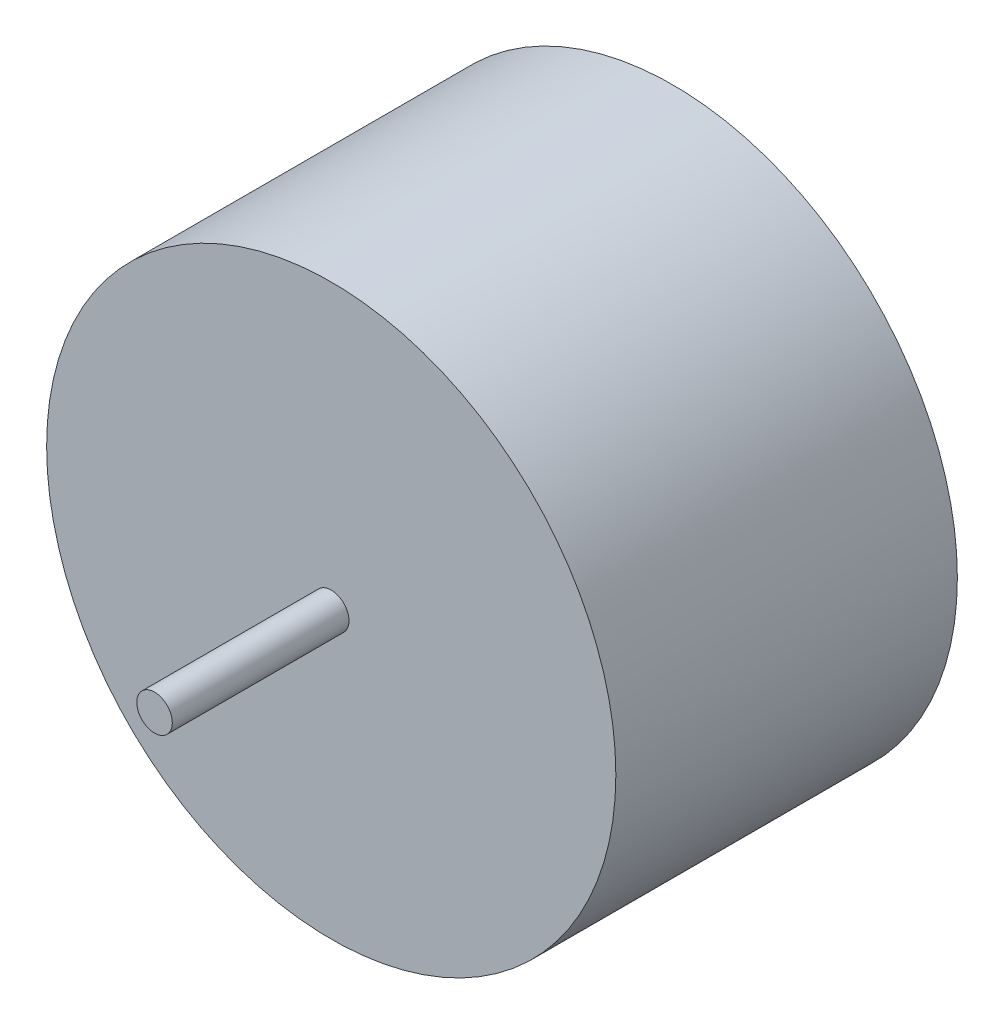
SolidWorks part; units mm, degrees
material "Plain Carbon Steel"
ref_plane "Front Plane" through (0, 0, 0) normal (0, 0, 1) x (1, 0, 0)
ref_plane "Top Plane" through (0, 0, 0) normal (0, 1, 0) x (1, 0, 0)
ref_plane "Right Plane" through (0, 0, 0) normal (1, 0, 0) x (0, 0, -1)
sketch "Sketch2" plane through (0, 0, 0) normal (0, 0, 1) x (1, 0, 0)
  circle A0 centre (0, 0) radius 15.875
  dimension "D1" = 31.75
extrude "Boss-Extrude1" add sketch "Sketch2" along normal blind 28.9052
sketch "Sketch3" plane through (0, 0, 0) normal (0, 0, 1) x (1, 0, 0)
  circle A0 centre (0, 0) radius 0.9906
  dimension "D1" = 1.9812
extrude "Cut-Extrude1" cut sketch "Sketch3" against normal blind 9.8552 from offset 28.9052 flip side to cut
